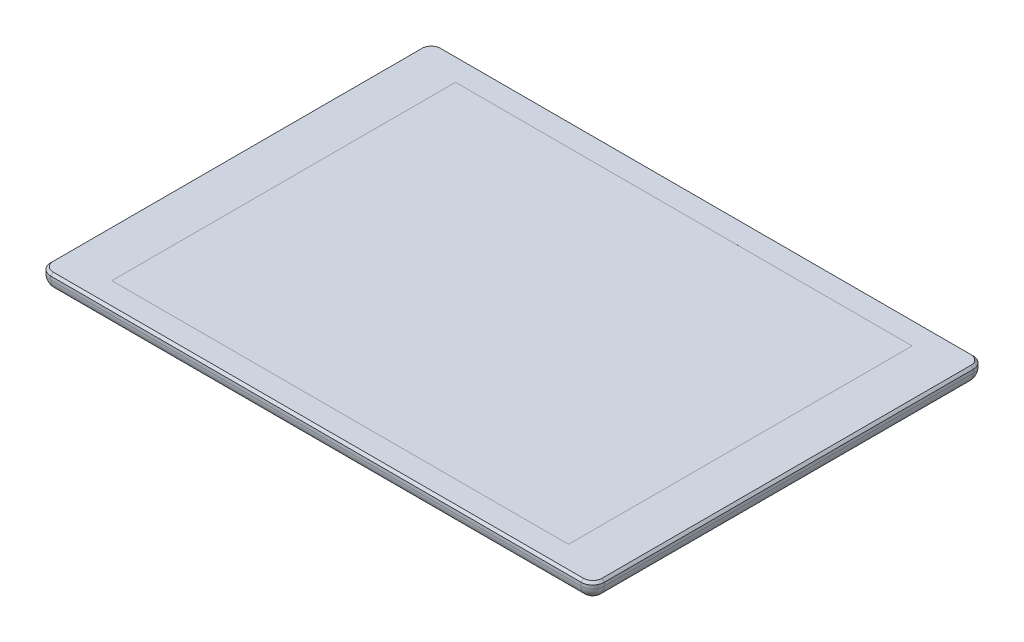
SolidWorks part; units mm, degrees
ref_plane "Front Plane" through (0, 0, 0) normal (0, 0, 1) x (1, 0, 0)
ref_plane "Top Plane" through (0, 0, 0) normal (0, 1, 0) x (1, 0, 0)
ref_plane "Right Plane" through (0, 0, 0) normal (1, 0, 0) x (0, 0, -1)
sketch "Sketch1" plane through (0, 0, 0) normal (0, 1, 0) x (1, 0, 0)
  line L1 (5, 0) -> (235, 0)
  line L2 (0, 5) -> (0, 165)
  line L3 (5, 170) -> (235, 170)
  line L4 (240, 5) -> (240, 165)
  arc A0 (0, 5) -> (5, 0) centre (5, 5) ccw
  arc A1 (235, 0) -> (240, 5) centre (235, 5) ccw
  arc A2 (240, 165) -> (235, 170) centre (235, 165) ccw
  arc A3 (5, 170) -> (0, 165) centre (5, 165) ccw
  point P7 (0, 0)
  point P10 (240, 0)
  point P15 (0, 170)
  dimension "D3" = 5
  dimension "D1" = 240
  dimension "D2" = 170
extrude "Boss-Extrude1" add sketch "Sketch1" along normal blind 7.5
fillet "Fillet1" radius 5 8 edges at (120, 0, 0) (238.5355, 0, -1.4645) (240, 0, -85) (238.5355, 0, -168.5355) (120, 0, -170) (1.4645, 0, -168.5355) (0, 0, -85) (1.4645, 0, -1.4645)
chamfer "Chamfer1" distance 1 angle 45 8 edges at (0, 7.5, -85) (1.4645, 7.5, -168.5355) (120, 7.5, -170) (238.5355, 7.5, -168.5355) (240, 7.5, -85) (238.5355, 7.5, -1.4645) (120, 7.5, 0) (1.4645, 7.5, -1.4645)
sketch "Sketch2" plane through (0, 7.5, 0) normal (0, 1, 0) x (1, 0, 0)
  line L0 (0, 5) -> (0, 165) construction
  line L1 (21, 10.5) -> (219, 10.5)
  line L2 (21, 10.5) -> (21, 159.5)
  line L3 (21, 159.5) -> (219, 159.5)
  line L4 (219, 10.5) -> (219, 159.5)
  line L5 (5, 170) -> (235, 170) construction
  line L6 (235, 0) -> (5, 0) construction
  line L7 (240, 165) -> (240, 5) construction
  dimension "D1" = 21
  dimension "D2" = 10.5
  dimension "D3" = 10.5
  dimension "D4" = 21
extrude "Cut-Extrude1" cut sketch "Sketch2" against normal blind 0.0001
